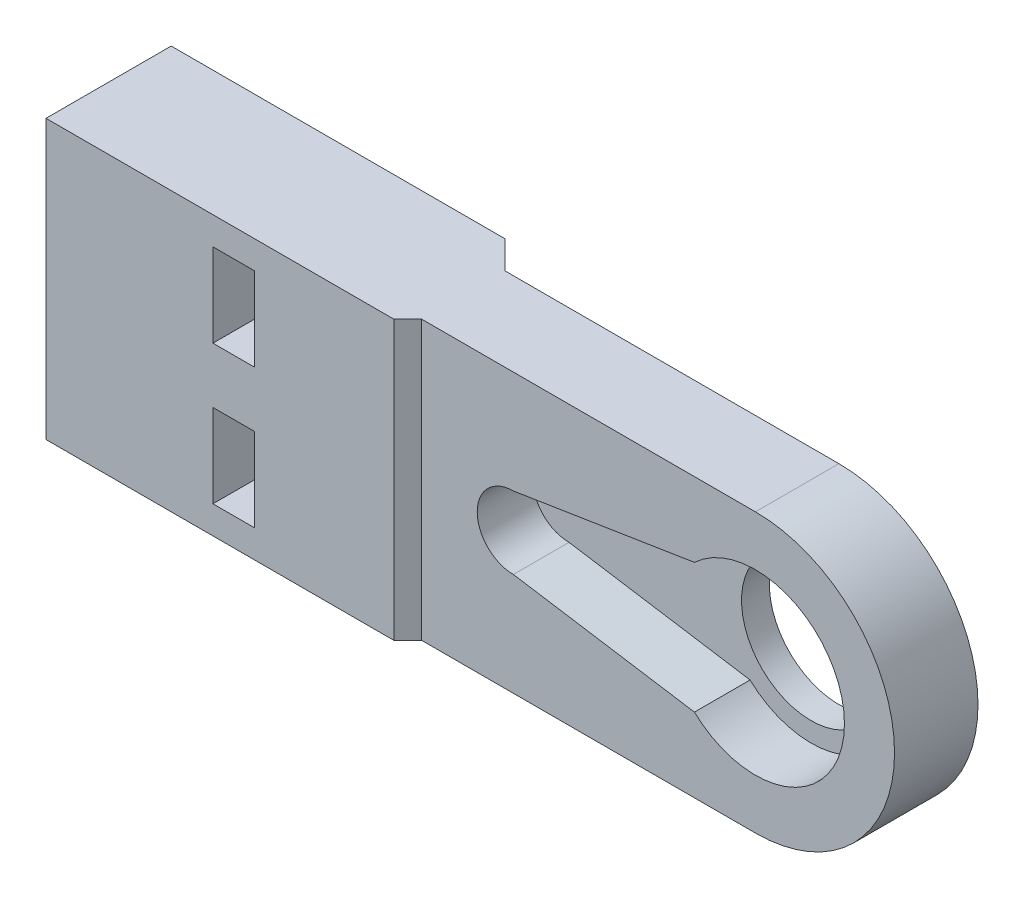
SolidWorks part; units mm, degrees
ref_plane "Спереди" through (0, 0, 0) normal (0, 0, 1) x (1, 0, 0)
ref_plane "Сверху" through (0, 0, 0) normal (0, 1, 0) x (1, 0, 0)
ref_plane "Справа" through (0, 0, 0) normal (1, 0, 0) x (0, 0, -1)
sketch "Эскиз1" plane through (0, 0, 0) normal (0, 0, 1) x (1, 0, 0)
  line L0 (0, 0) -> (-50, 0) construction
  line L2 (0, 10) -> (-50, 10)
  line L3 (0, 10) -> (0, -10)
  line L4 (0, -10) -> (-50, -10)
  line L5 (-50, 10) -> (-50, -10)
  circle A0 centre (0, 0) radius 10
  circle A1 centre (0, 0) radius 5
  dimension "D2" = 20
  dimension "D3" = 10
  dimension "D1" = 50
extrude "Бобышка-Вытянуть1" add sketch "Эскиз1" along normal blind 6 contours A1 L3 A0 | L0 A1 L3 A0 | A1 L0 A0 L3 | A0 L0 L5 L4 | L0 A0 L2 L5
sketch "Эскиз2" plane through (0, 0, 6) normal (0, 0, 1) x (1, 0, 0)
  line L0 (0, 0) -> (-17.4, 0) construction
  line L1 (-17.4, 2.6) -> (-4.3855, 4.6613)
  line L2 (-17.4, -2.6) -> (-4.3855, -4.6613)
  circle A0 centre (0, 0) radius 6.4
  circle A1 centre (-17.4, 0) radius 2.6
  dimension "D2" = 12.8
  dimension "D3" = 5.2
  dimension "D1" = 17.4
  dimension "D4" = 18
extrude "Вырез-Вытянуть1" cut sketch "Эскиз2" against normal blind 4
sketch "Эскиз3" plane through (-50, 0, 0) normal (-1, 0, 0) x (0, 0, 1)
  line L0 (6, 10) -> (6, -10) construction
  line L1 (6, 10) -> (6, -10)
  line L2 (6, 0) -> (0, 0) construction
  line L3 (0, 10) -> (0, -10) construction
  line L4 (0, 10) -> (0, -10)
  circle A0 centre (2.2, 5) radius 1.5
  circle A1 centre (2.2, -5) radius 1.5
  dimension "D1" = 10
  dimension "D2" = 3
  dimension "D3" = 2.2
extrude "Вырез-Вытянуть2" cut sketch "Эскиз3" against normal blind 20 contours A0 | A1
sketch "Эскиз4" plane through (0, 0, 0) normal (0, 1, 0) x (1, 0, 0)
  line L0 (0, 0) -> (-50, 0) construction
  line L1 (0, 0) -> (-50, 0)
  line L2 (-50, 0) -> (-50, 2)
  line L3 (-50, 2) -> (-26, 2)
  line L4 (-26, 2) -> (-24, 0)
  dimension "D1" = 2
  dimension "D2" = 135
  dimension "D3" = 24
extrude "Бобышка-Вытянуть2" add sketch "Эскиз4" along normal mid plane 20 contours L4 L3 L2 L1
sketch "Эскиз6" plane through (0, 0, 0) normal (0, 1, 0) x (1, 0, 0)
  line L0 (-26, 2) -> (-24, 0) construction
  line L1 (-26, 2) -> (-24, 0)
  line L2 (-50, -6) -> (-50, 2) construction
  line L3 (-50, -6) -> (-50, 2)
  line L4 (-50, -6) -> (-50, -7)
  line L5 (-50, -7) -> (-25, -7)
  line L6 (-25, -7) -> (-24, -6)
  line L7 (0, -6) -> (-50, -6) construction
  line L8 (0, -6) -> (-50, -6)
  dimension "D1" = 1
  dimension "D2" = 135
extrude "Бобышка-Вытянуть3" add sketch "Эскиз6" along normal mid plane 20 contours L6 L8 L4 L5
sketch "Эскиз5" plane through (0, 0, -2) normal (0, 0, -1) x (-1, 0, 0)
  line L0 (50, 0) -> (26, 0) construction
  line L1 (50, 10) -> (50, -10) construction
  line L2 (26, 10) -> (26, -10) construction
  line L3 (35, -5) -> (38, -5) construction
  line L4 (38, -8) -> (35, -8)
  line L5 (38, -8) -> (38, -2)
  line L6 (38, -2) -> (35, -2)
  line L7 (35, -8) -> (35, -2)
  line L8 (38, 8) -> (35, 8)
  line L9 (38, 8) -> (38, 2)
  line L10 (38, 2) -> (35, 2)
  line L11 (35, 8) -> (35, 2)
  line L12 (38, 5) -> (35, 5) construction
  dimension "D1" = 6
  dimension "D2" = 6
  dimension "D3" = 5
  dimension "D4" = 3
  dimension "D5" = 3
  dimension "D6" = 15
extrude "Вырез-Вытянуть3" cut sketch "Эскиз5" against normal through all
